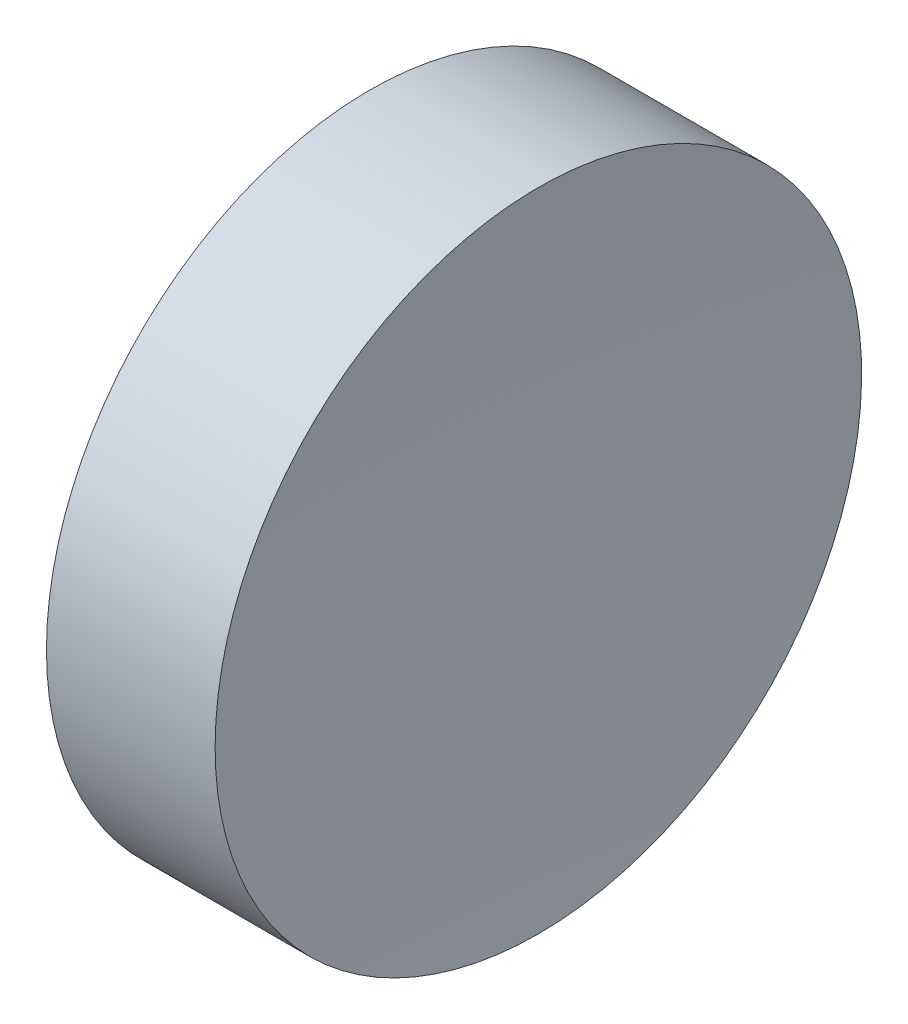
SolidWorks part; units mm, degrees
ref_plane "前视基准面" through (0, 0, 0) normal (0, 0, 1) x (1, 0, 0)
ref_plane "上视基准面" through (0, 0, 0) normal (0, 1, 0) x (1, 0, 0)
ref_plane "右视基准面" through (0, 0, 0) normal (1, 0, 0) x (0, 0, -1)
sketch "草图1" plane through (0, 0, 0) normal (0, 0, 1) x (1, 0, 0)
  line L0 (108.9851, 69.378) -> (132.7763, 69.378) construction
  line L1 (115.0927, 69.378) -> (115.0927, 81.878)
  line L2 (115.0927, 81.878) -> (121.6144, 81.878)
  line L3 (121.0927, 69.378) -> (115.0927, 69.378)
  arc A0 (121.6144, 81.878) -> (121.0927, 69.378) centre (271.0927, 69.378) ccw
revolve "旋转1" add sketch "草图1" angle 360 about L0
